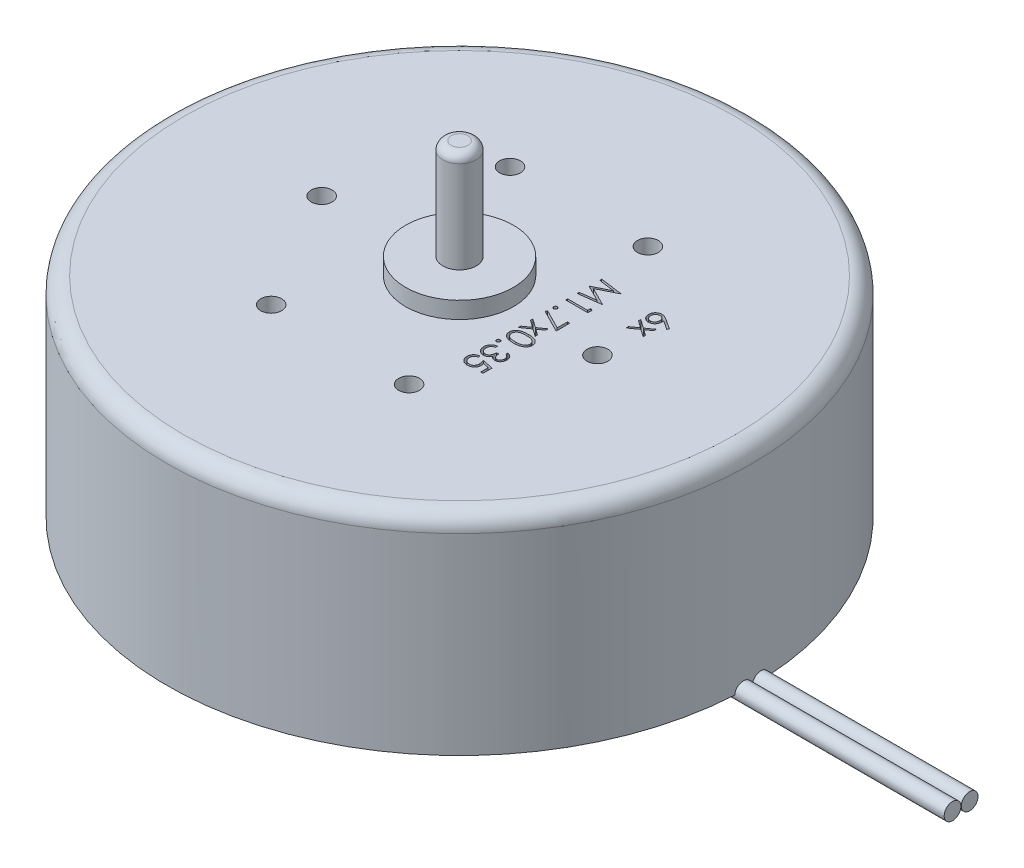
SolidWorks part; units mm, degrees
ref_plane "Ebene vorne" through (0, 0, 0) normal (0, 0, 1) x (1, 0, 0)
ref_plane "Ebene oben" through (0, 0, 0) normal (0, 1, 0) x (1, 0, 0)
ref_plane "Ebene rechts" through (0, 0, 0) normal (1, 0, 0) x (0, 0, -1)
sketch "Skizze1" plane through (0, 0, 0) normal (0, 1, 0) x (1, 0, 0)
  circle A0 centre (0, 0) radius 17.5
  dimension "D1" = 35
extrude "Aufsatz-Linear austragen1" add sketch "Skizze1" along normal blind 12.5
sketch "Skizze2" plane through (0, 12.5, 0) normal (0, 1, 0) x (1, 0, 0)
  circle A0 centre (0, 0) radius 3.225
  dimension "D1" = 6.45
extrude "Aufsatz-Linear austragen2" add sketch "Skizze2" along normal blind 1
sketch "Skizze3" plane through (0, 12.5, 0) normal (0, 1, 0) x (1, 0, 0)
  circle A0 centre (0, 0) radius 1
  dimension "D1" = 2
extrude "Aufsatz-Linear austragen3" add sketch "Skizze3" along normal blind 7
fillet "Verrundung1" radius 0.5 1 edges at (0, 19.5, 1)
sketch "Skizze4" plane through (0, 0, 0) normal (0, -1, 0) x (1, 0, 0)
  circle A0 centre (0, 0) radius 3.05
  dimension "D1" = 6.1
extrude "Aufsatz-Linear austragen4" add sketch "Skizze4" along normal blind 0.5
fillet "Verrundung2" radius 1 1 edges at (0, 12.5, 17.5)
sketch "Skizze5" plane through (0, 12.5, 0) normal (0, 1, 0) x (1, 0, 0)
  circle A0 centre (0, 0) radius 8.25 construction
  point P3 (8.25, 0)
  dimension "D1" = 16.5
hole_wizard "M1.6 Gewindebohrung1" positions "Skizze7" profile "Skizze6" tap size "M1.6" standard "DIN"
sketch "Skizze7" plane through (0, 12.5, 0) normal (0, 1, 0) x (1, 0, 0)
  point P0 (8.25, 0)
sketch "Skizze6" plane through (8.25, 12.5, 0) normal (1, 0, 0) x (0, 0, 1)
  line L0 (0, 0) -> (0, 5.3255)
  line L1 (0, 5.3255) -> (0.625, 4.95)
  line L2 (0.625, 4.95) -> (0.625, 0)
  line L5 (0.625, 0) -> (0, 0)
  line L10 (0, 5.3255) -> (-0.625, 4.95) construction
  line L11 (0, -6.35) -> (0, 107.95) construction
  dimension "Bohrerdurchmesser" = 1.25
  dimension "Bohrungstiefe" = 4.95
  dimension "Spitzenwinkel" = 118
cosmetic thread "Bohrungsgewinde1" parameters "D1"=3.2, "D2"=1.6
pattern_circular "Kreismuster1" count 6 over 360 about axis through (0, 0, 0) along (0, 1, 0) of "M1.6 Gewindebohrung1"
sketch "Skizze8" plane through (0, 12.5, 0) normal (0, 1, 0) x (1, 0, 0)
  line L0 (7.6973, 4.1692) -> (7.6973, -4.645) construction
  text T0 "6x\r\nM1.7x0.35\r\n" font "Century Gothic" height in points 5
extrude "Schnitt-Linear austragen1" cut sketch "Skizze8" against normal blind 0.5
sketch "Skizze9" plane through (0, 0, 0) normal (1, 0, 0) x (0, 0, -1)
  line L0 (-3.05, 0) -> (3.05, 0) construction
  circle A0 centre (0.5232, 0) radius 0.5
  circle A1 centre (-0.5, 0) radius 0.5
  dimension "D1" = 1
extrude "Aufsatz-Linear austragen8" add sketch "Skizze9" along normal blind 30
